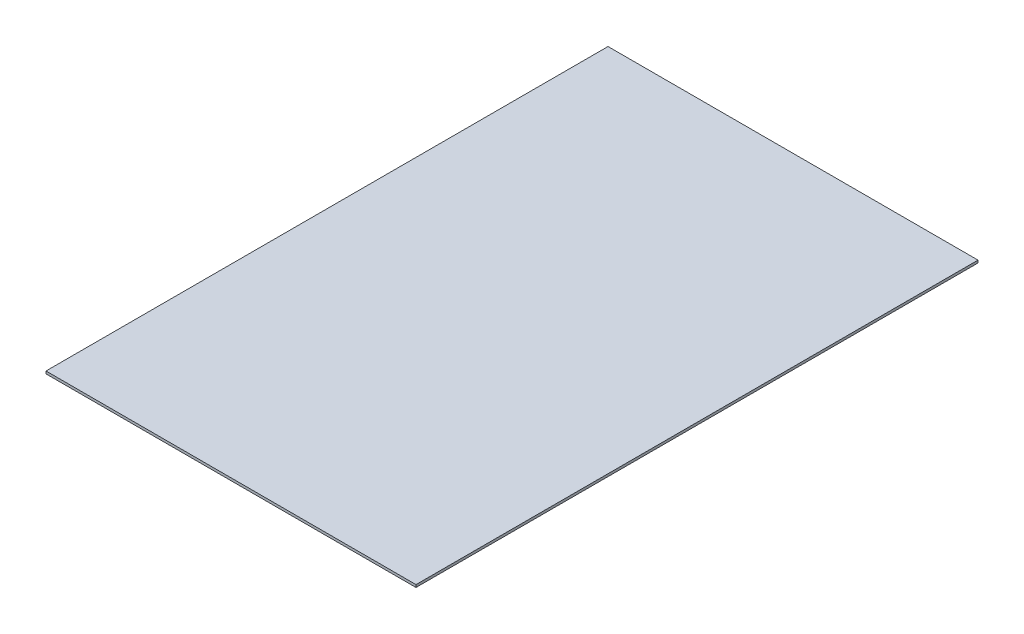
SolidWorks part; units mm, degrees
material "PVC Rigid"
ref_plane "Front Plane" through (0, 0, 0) normal (0, 0, 1) x (1, 0, 0)
ref_plane "Top Plane" through (0, 0, 0) normal (0, 1, 0) x (1, 0, 0)
ref_plane "Right Plane" through (0, 0, 0) normal (1, 0, 0) x (0, 0, -1)
sketch "Sketch1" plane through (0, 0, 0) normal (0, 1, 0) x (1, 0, 0)
  line L1 (0, 0) -> (440, 0)
  line L2 (0, 0) -> (0, 668.38)
  line L3 (0, 668.38) -> (440, 668.38)
  line L4 (440, 0) -> (440, 668.38)
  dimension "D1" = 440
  dimension "D2" = 668.38
extrude "Boss-Extrude1" add sketch "Sketch1" along normal blind 3
